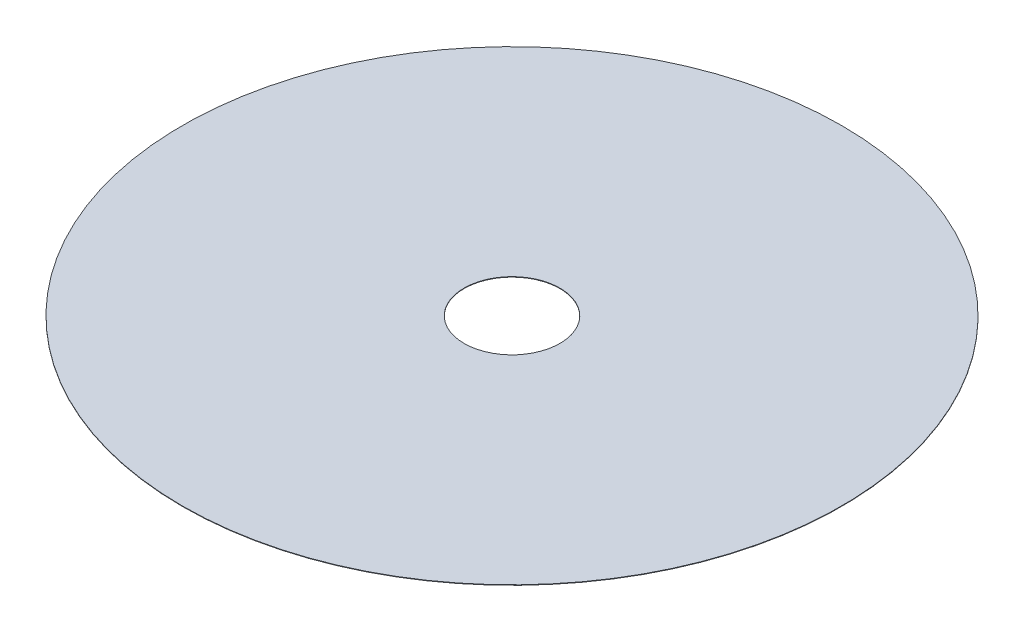
SolidWorks part; units mm, degrees
ref_plane "Front Plane" through (0, 0, 0) normal (0, 0, 1) x (1, 0, 0)
ref_plane "Top Plane" through (0, 0, 0) normal (0, 1, 0) x (1, 0, 0)
ref_plane "Right Plane" through (0, 0, 0) normal (1, 0, 0) x (0, 0, -1)
sketch "Sketch1" plane through (0, 0, 0) normal (0, 1, 0) x (1, 0, 0)
  circle A0 centre (0, 0) radius 27500
  dimension "D1" = 55000
extrude "Boss-Extrude1" add sketch "Sketch1" along normal blind 38.1
sketch "Sketch2" plane through (0, 38.1, 0) normal (0, 1, 0) x (1, 0, 0)
  circle A0 centre (0, 0) radius 4000
  dimension "D1" = 8000
extrude "Cut-Extrude1" cut sketch "Sketch2" against normal blind 38.1
